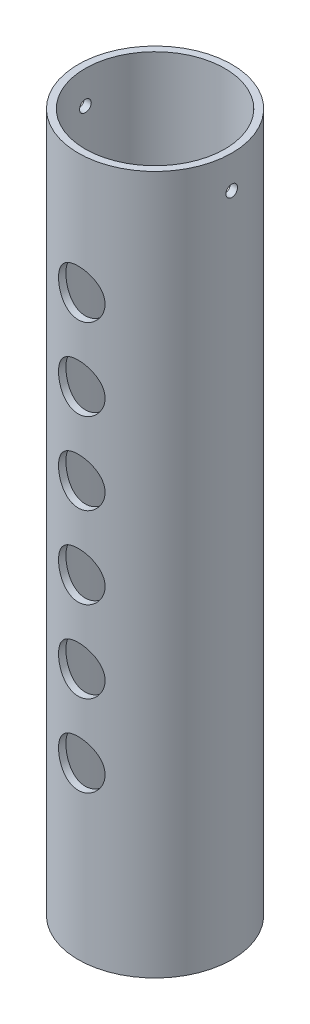
SolidWorks part; units mm, degrees
ref_plane "Alzado" through (0, 0, 0) normal (0, 0, 1) x (1, 0, 0)
ref_plane "Planta" through (0, 0, 0) normal (0, 1, 0) x (1, 0, 0)
ref_plane "Vista lateral" through (0, 0, 0) normal (1, 0, 0) x (0, 0, -1)
sketch "Sketch1" plane through (0, 0, 0) normal (0, 1, 0) x (1, 0, 0)
  circle A0 centre (0, 0) radius 30
  dimension "D1" = 60
extrude "Extrude-Thin1" add sketch "Sketch1" along normal blind 300 thin
sketch "Sketch2" plane through (0, 0, 0) normal (0, 0, 1) x (1, 0, 0)
  line L0 (0, 300) -> (0, 0) construction
  line L1 (33, 300) -> (-33, 300) construction
  circle A0 centre (0, 248) radius 10
  dimension "D1" = 20
  dimension "D2" = 52
extrude "Cut-Extrude1" cut sketch "Sketch2" against normal through all and the other way through all
pattern_linear "LPattern1" count 6 spacing 35 along (0, -1, 0) of "Cut-Extrude1"
sketch "Sketch3" plane through (0, 0, 0) normal (1, 0, 0) x (0, 0, -1)
  line L0 (0, 300) -> (0, 0) construction
  line L1 (33, 300) -> (-33, 300) construction
  circle A0 centre (0, 286) radius 2.5
  dimension "D1" = 5
  dimension "D2" = 14
extrude "Cut-Extrude2" cut sketch "Sketch3" against normal through all and the other way through all
cosmetic thread "Cosmetic Thread1" parameters "D2"=6
cosmetic thread "Cosmetic Thread2" parameters "D2"=6
